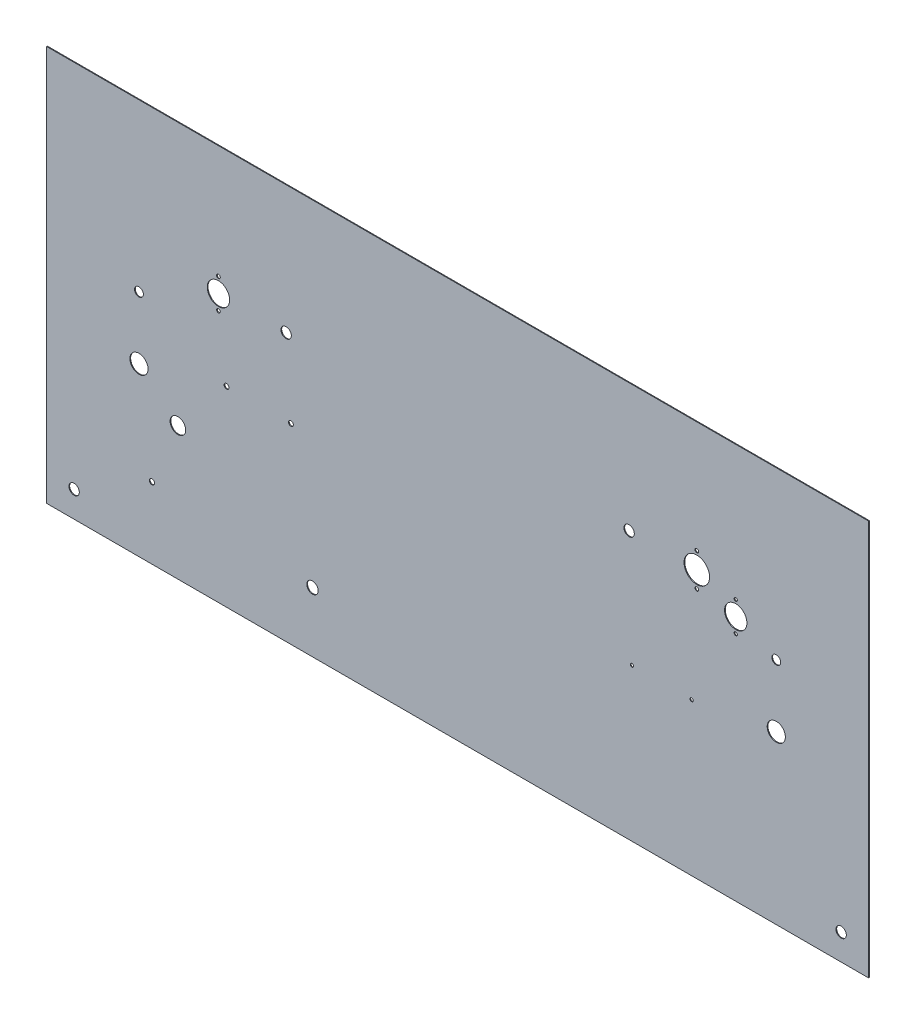
SolidWorks part; units mm, degrees
ref_plane "Front Plane" through (0, 0, 0) normal (0, 0, 1) x (1, 0, 0)
ref_plane "Top Plane" through (0, 0, 0) normal (0, 1, 0) x (1, 0, 0)
ref_plane "Right Plane" through (0, 0, 0) normal (1, 0, 0) x (0, 0, -1)
sketch "Base Sketch" plane through (0, 0, 0) normal (0, 0, 1) x (1, 0, 0)
  line L0 (0, 0) -> (750.8875, 0) construction
  line L1 (375.4437, 0) -> (375.4437, 236.5375) construction
  line L2 (543.3219, 236.5375) -> (207.5656, 236.5375) construction
  line L3 (-26.9875, -25.4) -> (777.875, -25.4)
  line L4 (375.4437, 0) -> (375.4437, -25.4) construction
  line L5 (375.4437, 236.5375) -> (375.4437, 361.95) construction
  line L6 (375.4437, 361.95) -> (-26.9875, 361.95) construction
  line L7 (-1.5875, -25.4) -> (375.4437, -25.4) construction
  line L8 (-1.5875, -25.4) -> (-1.5875, 152.4) construction
  line L9 (-1.5875, 152.4) -> (375.4437, 152.4) construction
  line L10 (375.4437, -25.4) -> (375.4437, 152.4) construction
  line L11 (23.8125, -25.4) -> (375.4437, -25.4) construction
  line L12 (23.8125, -25.4) -> (23.8125, 203.2) construction
  line L13 (23.8125, 203.2) -> (375.4437, 203.2) construction
  line L14 (375.4437, -25.4) -> (375.4437, 203.2) construction
  line L15 (49.2125, -25.4) -> (375.4437, -25.4) construction
  line L16 (49.2125, -25.4) -> (49.2125, 228.6) construction
  line L17 (49.2125, 228.6) -> (375.4437, 228.6) construction
  line L18 (375.4437, -25.4) -> (375.4437, 228.6) construction
  line L19 (74.6125, -25.4) -> (375.4437, -25.4) construction
  line L20 (74.6125, -25.4) -> (74.6125, 254) construction
  line L21 (74.6125, 254) -> (375.4437, 254) construction
  line L22 (375.4437, -25.4) -> (375.4437, 254) construction
  line L23 (100.0125, -25.4) -> (375.4437, -25.4) construction
  line L24 (100.0125, -25.4) -> (100.0125, 276.225) construction
  line L25 (100.0125, 276.225) -> (375.4437, 276.225) construction
  line L26 (375.4437, -25.4) -> (375.4437, 276.225) construction
  line L27 (125.4125, -25.4) -> (375.4437, -25.4) construction
  line L28 (125.4125, -25.4) -> (125.4125, 292.1) construction
  line L29 (125.4125, 292.1) -> (375.4437, 292.1) construction
  line L30 (375.4437, -25.4) -> (375.4437, 292.1) construction
  line L31 (150.8125, -25.4) -> (375.4437, -25.4) construction
  line L32 (150.8125, -25.4) -> (150.8125, 301.625) construction
  line L33 (150.8125, 301.625) -> (375.4437, 301.625) construction
  line L34 (375.4437, -25.4) -> (375.4437, 301.625) construction
  line L35 (176.2125, -25.4) -> (375.4437, -25.4) construction
  line L36 (176.2125, -25.4) -> (176.2125, 314.325) construction
  line L37 (176.2125, 314.325) -> (375.4437, 314.325) construction
  line L38 (375.4437, -25.4) -> (375.4437, 314.325) construction
  line L39 (201.6125, -25.4) -> (375.4437, -25.4) construction
  line L40 (201.6125, -25.4) -> (201.6125, 322.2625) construction
  line L41 (201.6125, 322.2625) -> (375.4437, 322.2625) construction
  line L42 (375.4437, -25.4) -> (375.4437, 322.2625) construction
  line L43 (227.0125, -25.4) -> (375.4437, -25.4) construction
  line L44 (227.0125, -25.4) -> (227.0125, 330.2) construction
  line L45 (227.0125, 330.2) -> (375.4437, 330.2) construction
  line L46 (375.4437, -25.4) -> (375.4437, 330.2) construction
  line L47 (252.4125, -25.4) -> (375.4437, -25.4) construction
  line L48 (252.4125, -25.4) -> (252.4125, 338.1375) construction
  line L49 (252.4125, 338.1375) -> (375.4437, 338.1375) construction
  line L50 (375.4437, -25.4) -> (375.4437, 338.1375) construction
  line L51 (277.8125, -25.4) -> (375.4437, -25.4) construction
  line L52 (277.8125, -25.4) -> (277.8125, 349.25) construction
  line L53 (277.8125, 349.25) -> (375.4437, 349.25) construction
  line L54 (375.4437, -25.4) -> (375.4437, 349.25) construction
  line L55 (-26.9875, -25.4) -> (-26.9875, 361.95) construction
  line L56 (-26.9875, -25.4) -> (-26.9875, 361.95)
  line L57 (-26.9875, 361.95) -> (777.875, 361.95)
  line L58 (777.875, 361.95) -> (777.875, -25.4)
  circle A0 centre (0, 0) radius 5.08
  circle A1 centre (750.8875, 0) radius 5.08
  circle A2 centre (207.5656, 236.5375) radius 5.08
  circle A3 centre (543.3219, 236.5375) radius 5.08
  arc A4 (-26.9875, -25.4) -> (777.875, -25.4) centre (375.4437, -47.434) cw construction
  point P9 (375.4437, 236.5375)
  point P54 (777.875, 434.5217)
  dimension "D1" = 10.16
  dimension "D2" = 750.8875
  dimension "D3" = 236.5375
  dimension "D4" = 335.7562
  dimension "D5" = 25.4
  dimension "D6" = 26.9875
  dimension "D7" = 387.35
  dimension "D8" = 25.4
  dimension "D9" = 177.8
  dimension "D10" = 50.8
  dimension "D11" = 228.6
  dimension "D12" = 76.2
  dimension "D13" = 254
  dimension "D14" = 101.6
  dimension "D15" = 279.4
  dimension "D16" = 127
  dimension "D17" = 301.625
  dimension "D18" = 152.4
  dimension "D19" = 317.5
  dimension "D20" = 177.8
  dimension "D21" = 327.025
  dimension "D22" = 203.2
  dimension "D23" = 339.725
  dimension "D24" = 228.6
  dimension "D25" = 347.6625
  dimension "D26" = 254
  dimension "D27" = 355.6
  dimension "D28" = 279.4
  dimension "D29" = 363.5375
  dimension "D30" = 304.8
  dimension "D31" = 374.65
extrude "Base w Mount Holes" add sketch "Base Sketch" along normal blind 0.7366
sketch "Throttle and Choke Cutout Sketch" plane through (0, 0, 0.7366) normal (0, 0, 1) x (1, 0, 0)
  line L0 (375.4438, -25.4) -> (375.4437, 361.95) construction
  line L1 (-26.9875, 361.95) -> (777.875, 361.95) construction
  line L2 (63.5, 199.0725) -> (63.5, 138.1125) construction
  line L3 (-26.9875, -25.4) -> (777.875, -25.4) construction
  line L4 (687.3875, 199.0725) -> (687.3875, 138.1125) construction
  circle A1 centre (63.5, 138.1125) radius 8.89
  circle A2 centre (63.5, 199.0725) radius 4.318
  circle A6 centre (687.3875, 199.0725) radius 4.318
  circle A7 centre (687.3875, 138.1125) radius 8.89
  point P4 (375.4437, 361.95)
  dimension "D1" = 17.78
  dimension "D2" = 8.636
  dimension "D3" = 63.5
  dimension "D4" = 138.1125
  dimension "D5" = 199.0725
extrude "Throttle and Choke Cutouts" cut sketch "Throttle and Choke Cutout Sketch" against normal through all
sketch "Starter Relay Mount Sketch" plane through (0, 0, 0.7366) normal (0, 0, 1) x (1, 0, 0)
  line L0 (149.225, 161.925) -> (212.217, 161.925) construction
  circle A0 centre (149.225, 161.925) radius 2.3813
  circle A1 centre (212.217, 161.925) radius 2.3813
  dimension "D2" = 4.7625
  dimension "D1" = 62.992
  dimension "D3" = 149.225
  dimension "D4" = 161.925
extrude "Starter Relay Mount" cut sketch "Starter Relay Mount Sketch" against normal through all
sketch "Oil Pressure Sender Clamp Mount Sketch" plane through (0, 0, 0.7366) normal (0, 0, 1) x (1, 0, 0)
  circle A0 centre (76.2, 44.45) radius 2.54
  dimension "D1" = 5.08
  dimension "D2" = 76.2
  dimension "D3" = 44.45
extrude "Oil Pressure Sender Clamp Mount" cut sketch "Oil Pressure Sender Clamp Mount Sketch" against normal through all contours A0
sketch "Starter Power Cutout Sketch" plane through (0, 0, 0.7366) normal (0, 0, 1) x (1, 0, 0)
  circle A0 centre (233.3625, 33.3375) radius 5.588
  dimension "D1" = 11.176
  dimension "D2" = 233.3625
  dimension "D3" = 33.3375
extrude "Starter Power Cutout" cut sketch "Starter Power Cutout Sketch" against normal through all
sketch "Fuel Return Cutout Sketch" plane through (0, 0, 0.7366) normal (0, 0, 1) x (1, 0, 0)
  circle A0 centre (101.6, 104.775) radius 7.62
  dimension "D3" = 15.24
  dimension "D1" = 101.6
  dimension "D2" = 104.775
extrude "Fuel Return Cutout" cut sketch "Fuel Return Cutout Sketch" against normal through all
sketch "Brake Master Cyl Mount Sketch" plane through (0, 0, 0.7366) normal (0, 0, 1) x (1, 0, 0)
  line L0 (546.1, 123.825) -> (604.52, 123.825) construction
  circle A0 centre (546.1, 123.825) radius 1.6256
  circle A1 centre (604.52, 123.825) radius 1.6256
  dimension "D1" = 3.2512
  dimension "D2" = 546.1
  dimension "D3" = 123.825
  dimension "D4" = 58.42
extrude "Brake Master Cyl Mount" cut sketch "Brake Master Cyl Mount Sketch" against normal through all
sketch "Cutout - AS012 - Instrumentation Right Sketch" plane through (0, 0, 0.7366) normal (0, 0, 1) x (1, 0, 0)
  line L0 (141.2875, 221.9871) -> (141.2875, 236.5375) construction
  line L1 (141.2875, 236.5375) -> (141.2875, 251.0879) construction
  line L2 (207.5656, 236.5375) -> (543.3219, 236.5375) construction
  line L3 (141.2875, 236.5375) -> (207.5656, 236.5375) construction
  circle A0 centre (141.2875, 236.5375) radius 10.9499
  circle A1 centre (141.2875, 221.9871) radius 1.8034
  circle A2 centre (141.2875, 251.0879) radius 1.8034
  dimension "D1" = 21.8999
  dimension "D2" = 3.6068
  dimension "D3" = 29.1008
  dimension "D4" = 141.2875
extrude "Cutout - AS012 - Instrumentation Right" cut sketch "Cutout - AS012 - Instrumentation Right Sketch" against normal through all
sketch "Cutout - AS014 - Tach and CDI Enables Left Sketch" plane through (0, 0, 0.7366) normal (0, 0, 1) x (1, 0, 0)
  line L0 (609.6, 220.2878) -> (609.6, 236.5375) construction
  line L1 (609.6, 236.5375) -> (609.6, 252.7871) construction
  line L2 (609.6, 236.5375) -> (543.3219, 236.5375) construction
  circle A0 centre (609.6, 236.5375) radius 12.4968
  circle A1 centre (609.6, 252.7871) radius 1.8034
  circle A2 centre (609.6, 220.2878) radius 1.8034
  dimension "D2" = 3.6068
  dimension "D3" = 24.9936
  dimension "D1" = 32.4993
  dimension "D4" = 609.6
extrude "Cutout - AS014 - Tach and CDI Enables Left" cut sketch "Cutout - AS014 - Tach and CDI Enables Left Sketch" against normal through all
sketch "Cutout - AS012 - Instrumentation Left Sketch" plane through (0, 0, 0.7366) normal (0, 0, 1) x (1, 0, 0)
  line L0 (647.7, 201.3496) -> (647.7, 215.9) construction
  line L1 (647.7, 215.9) -> (647.7, 230.4504) construction
  circle A0 centre (647.7, 215.9) radius 10.9499
  circle A1 centre (647.7, 230.4504) radius 1.6002
  circle A2 centre (647.7, 201.3496) radius 1.6002
  dimension "D1" = 21.8999
  dimension "D2" = 3.2004
  dimension "D3" = 29.1008
  dimension "D4" = 647.7
  dimension "D5" = 215.9
extrude "Cutout - AS012 - Instrumentation Left" cut sketch "Cutout - AS012 - Instrumentation Left Sketch" against normal through all
